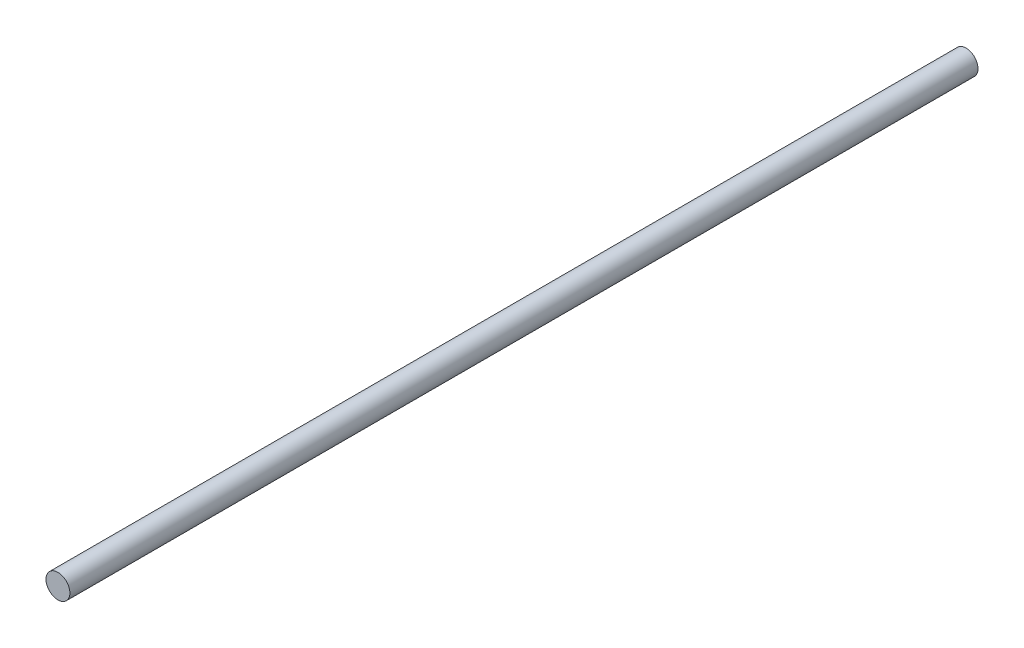
SolidWorks part; units mm, degrees
ref_plane "Front Plane" through (0, 0, 0) normal (0, 0, 1) x (1, 0, 0)
ref_plane "Top Plane" through (0, 0, 0) normal (0, 1, 0) x (1, 0, 0)
ref_plane "Right Plane" through (0, 0, 0) normal (1, 0, 0) x (0, 0, -1)
sketch "Sketch1" plane through (0, 0, 0) normal (0, 0, 1) x (1, 0, 0)
  circle A0 centre (0, 0) radius 5
  dimension "D1" = 10
extrude "Boss-Extrude1" add sketch "Sketch1" along normal blind 380 contours A0
